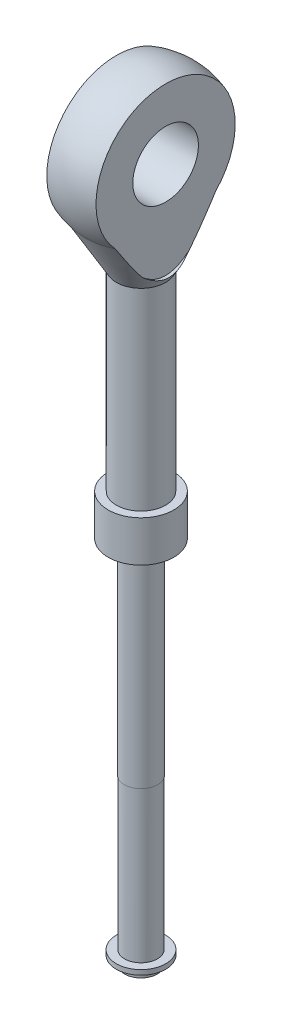
SolidWorks part; units mm, degrees
ref_plane "Płaszczyzna przednia" through (0, 0, 0) normal (0, 0, 1) x (1, 0, 0)
ref_plane "Płaszczyzna górna" through (0, 0, 0) normal (0, 1, 0) x (1, 0, 0)
ref_plane "Płaszczyzna prawa" through (0, 0, 0) normal (1, 0, 0) x (0, 0, -1)
sketch "Szkic1" plane through (0, 0, 0) normal (0, 0, 1) x (1, 0, 0)
  line L0 (0, 0) -> (0, 67.6259) construction
  line L1 (0, 0) -> (-2, 0)
  line L2 (-2, 0) -> (-2, 1.0092)
  line L3 (-2, 45) -> (-4, 45)
  line L4 (-4, 45) -> (-4, 50)
  line L5 (-4, 50) -> (-3, 50)
  line L6 (-3, 50) -> (-3, 73.52)
  line L7 (0, 95.004) -> (0, 76) construction
  line L8 (-3, 73.52) -> (-6.8112, 80.1212)
  line L9 (0, 95.004) -> (0, 88.504)
  line L10 (0, 83.504) -> (0, 0)
  line L14 (-2, 1.6005) -> (-2, 45)
  line L15 (-2, 1.0092) -> (-3.0148, 1.0092)
  line L16 (-3.0148, 1.0092) -> (-3.0148, 1.6005)
  line L17 (-3.0148, 1.6005) -> (-2, 1.6005)
  arc A0 (0, 95.004) -> (-6.8112, 80.1212) centre (0, 86.004) ccw
  arc A1 (0, 88.504) -> (0, 83.504) centre (0, 86.004) ccw
  point P11 (-4, 47.5)
  dimension "D1" = 18
  dimension "D5" = 5
  dimension "D2" = 4
  dimension "D3" = 8
  dimension "D4" = 6
  dimension "D6" = 30
  dimension "D7" = 45
  dimension "D8" = 5
  dimension "D9" = 23.52
revolve "Obrót1" add sketch "Szkic1" angle 360 about L10
sketch "Szkic2" plane through (0, 0, 0) normal (0, 1, 0) x (1, 0, 0)
  line L0 (0, 11.7218) -> (0, -11.8125) construction
  line L1 (-9.6119, -9) -> (-4, -9)
  line L2 (9.6119, 9) -> (4, 9)
  line L3 (9.6119, 9) -> (9.6119, -9)
  line L4 (9.6119, -9) -> (4, -9)
  line L5 (4, 9) -> (4, -9)
  line L6 (-4, 9) -> (-4, -9)
  line L7 (-9.6119, 9) -> (-4, 9)
  line L8 (-9.6119, 9) -> (-9.6119, -9)
  point P7 (4, 0)
  dimension "D1" = 18
  dimension "D2" = 4
extrude "Wytnij-wyciągnięcie3" cut sketch "Szkic2" along normal blind 200
sketch "Szkic3" plane through (-4, 0, 0) normal (-1, 0, 0) x (0, 0, 1)
  circle A0 centre (0, 86.004) radius 4
  arc A1 (5.5129, 80.1212) -> (-5.5129, 80.1212) centre (0, 86.004) ccw construction
  dimension "D1" = 8
extrude "Wytnij-wyciągnięcie4" cut sketch "Szkic3" against normal through all
sketch "Szkic4" plane through (-4, 0, 0) normal (-1, 0, 0) x (0, 0, 1)
  arc A6 (6.2707, 79.4616) -> (-6.2707, 79.4616) centre (0, 86.004) ccw
  arc A8 (6.2707, 79.4616) -> (-6.2707, 79.4616) centre (0, 86.004) ccw
  spline S3 degree 3 poles (-1639.2357, -1072.8375) (6.8188, 195.6028) (-31.276, 110.8264) (-4.5633, 77.2196) (-4.1064, 76.6816) (-3.3634, 75.9263) (-3.1068, 75.6847) (-2.5657, 75.2335) (-2.2785, 75.0226) (-1.6741, 74.6625) (-1.3565, 74.513) (-0.6767, 74.3038) (-0.3288, 74.2494) (0.2029, 74.2535) (0.3807, 74.2695) (0.7278, 74.3275) (0.8986, 74.3699) (1.2349, 74.4785) (1.4007, 74.5452) (1.7193, 74.6956) (1.8734, 74.7797) (2.3227, 75.0533) (2.6069, 75.2655) (3.1455, 75.72) (3.399, 75.961) (4.1303, 76.7093) (4.5805, 77.2405) (31.3706, 110.9886) (-4.8852, 198.5227) (1594.7006, -1133.4435) knots -7.369315 -7.369315 -7.369315 -7.369315 0.125 0.125 0.25 0.25 0.3125 0.3125 0.375 0.375 0.4375 0.4375 0.5 0.5 0.53125 0.53125 0.5625 0.5625 0.59375 0.59375 0.625 0.625 0.6875 0.6875 0.75 0.75 0.875 0.875 8.477722 8.477722 8.477722 8.477722 only from (-6.2707, 79.4616) to (6.2707, 79.4616)
  spline S4 degree 3 poles (-6.2707, 79.4616) (-5.8602, 78.888) (-5.4398, 78.3223) (-4.5633, 77.2196) (-4.1064, 76.6816) (-3.3634, 75.9263) (-3.1068, 75.6847) (-2.5657, 75.2335) (-2.2785, 75.0226) (-1.6741, 74.6625) (-1.3565, 74.513) (-0.6767, 74.3038) (-0.3288, 74.2494) (0.2029, 74.2535) (0.3807, 74.2695) (0.7278, 74.3275) (0.8986, 74.3699) (1.2349, 74.4785) (1.4007, 74.5452) (1.7193, 74.6956) (1.8734, 74.7797) (2.3227, 75.0533) (2.6069, 75.2655) (3.1455, 75.72) (3.399, 75.961) (4.1303, 76.7093) (4.5805, 77.2405) (5.4472, 78.3323) (5.8637, 78.8929) (6.2707, 79.4616) knots 0 0 0 0 0.125 0.125 0.25 0.25 0.3125 0.3125 0.375 0.375 0.4375 0.4375 0.5 0.5 0.53125 0.53125 0.5625 0.5625 0.59375 0.59375 0.625 0.625 0.6875 0.6875 0.75 0.75 0.875 0.875 1 1 1 1
  dimension "D1" = 1
extrude "Wytnij-wyciągnięcie5" cut sketch "Szkic4" against normal blind 1
mirror "Lustro1" about plane through (0, 0, 0) normal (1, 0, 0) of "Wytnij-wyciągnięcie5"
sketch "Szkic5" plane through (0, 45, 0) normal (0, -1, 0) x (1, 0, 0)
  circle A0 centre (0, 0) radius 2.025
  dimension "D1" = 4.05
extrude "Dodanie-wyciągnięcie1" add sketch "Szkic5" along normal blind 25
